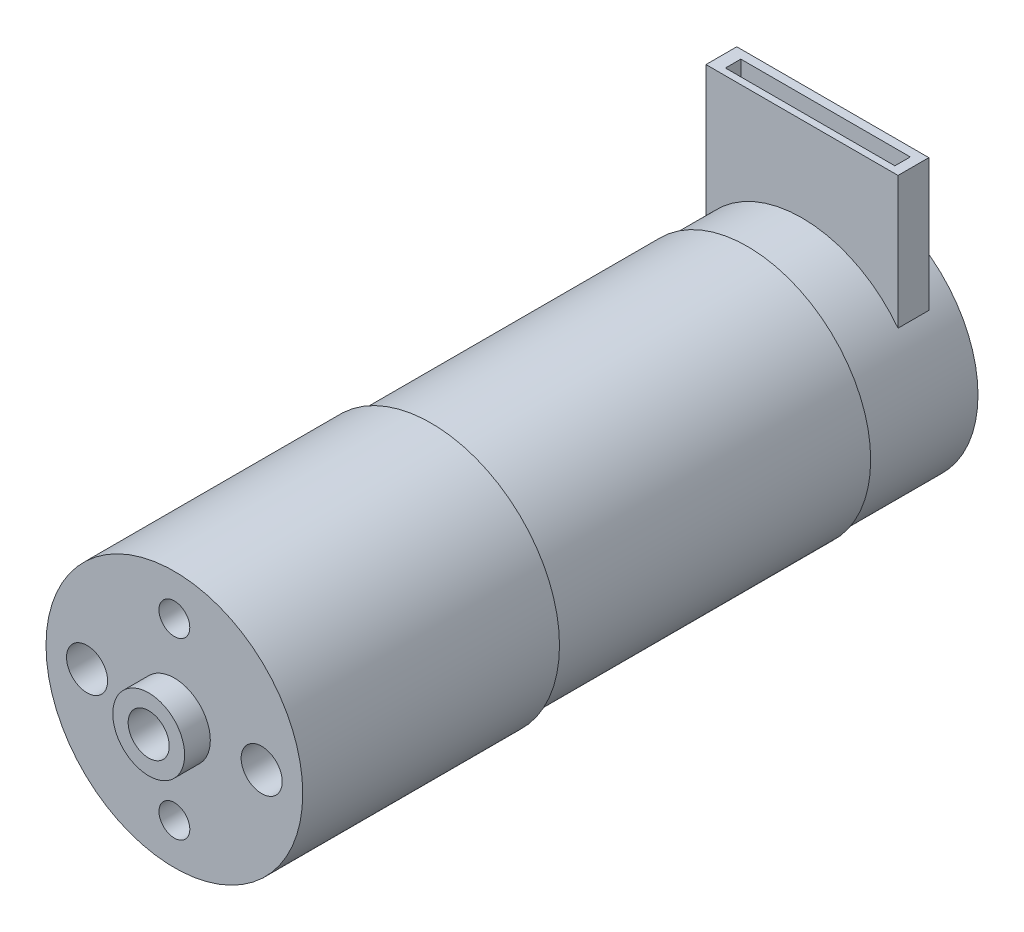
SolidWorks part; units mm, degrees
material "1060 Alloy"
ref_plane "Front Plane" through (0, 0, 0) normal (0, 0, 1) x (1, 0, 0)
ref_plane "Top Plane" through (0, 0, 0) normal (0, 1, 0) x (1, 0, 0)
ref_plane "Right Plane" through (0, 0, 0) normal (1, 0, 0) x (0, 0, -1)
sketch "Sketch1" plane through (0, 0, 0) normal (0, 0, 1) x (1, 0, 0)
  circle A0 centre (0, 0) radius 12
  dimension "D1" = 24
extrude "Boss-Extrude1" add sketch "Sketch1" along normal blind 30.8
sketch "Sketch2" plane through (0, 0, 30.8) normal (0, 0, 1) x (1, 0, 0)
  circle A0 centre (0, 0) radius 12.5
  dimension "D1" = 25
extrude "Boss-Extrude2" add sketch "Sketch2" along normal blind 25
sketch "Sketch3" plane through (0, 0, 55.8) normal (0, 0, 1) x (1, 0, 0)
  circle A0 centre (0, 0) radius 3.5
  dimension "D1" = 7
extrude "Boss-Extrude3" add sketch "Sketch3" along normal blind 2.5
sketch "Sketch4" plane through (0, 0, 58.3) normal (0, 0, 1) x (1, 0, 0)
  circle A0 centre (0, 0) radius 2
  dimension "D1" = 4
sketch "Sketch6" plane through (0, 0, 0) normal (0, 0, -1) x (-1, 0, 0)
  circle A0 centre (0, 0) radius 11.75
  dimension "D1" = 23.5
extrude "Boss-Extrude5" add sketch "Sketch6" along normal blind 10.7
sketch "Sketch7" plane through (0, 0, 0) normal (0, 1, 0) x (1, 0, 0)
  line L1 (9.3497, 8.3124) -> (-9.3497, 8.3124)
  line L2 (9.3497, 8.3124) -> (9.3497, 5.3124)
  line L3 (9.3497, 5.3124) -> (-9.3497, 5.3124)
  line L4 (-9.3497, 8.3124) -> (-9.3497, 5.3124)
  line L5 (9.3497, 8.3124) -> (-9.3497, 5.3124) construction
  line L6 (9.3497, 5.3124) -> (-9.3497, 8.3124) construction
  point P0 (0, 6.8124)
  dimension "D1" = 18.6994
  dimension "D2" = 3
extrude "Boss-Extrude6" add sketch "Sketch7" along normal blind 20
sketch "Sketch10" plane through (0, 20, 0) normal (0, 1, 0) x (1, 0, 0)
  line L1 (8.3873, 7.4684) -> (-8.1127, 7.4684)
  line L2 (8.3873, 7.4684) -> (8.3873, 5.9684)
  line L3 (8.3873, 5.9684) -> (-8.1127, 5.9684)
  line L4 (-8.1127, 7.4684) -> (-8.1127, 5.9684)
  line L5 (8.3873, 7.4684) -> (-8.1127, 5.9684) construction
  line L6 (8.3873, 5.9684) -> (-8.1127, 7.4684) construction
  point P0 (0.1373, 6.7184)
  dimension "D1" = 16.5
  dimension "D2" = 1.5
extrude "Cut-Extrude4" cut sketch "Sketch10" against normal blind 10
extrude "Cut-Extrude7" cut sketch "Sketch4" against normal blind 10
sketch "Sketch11" plane through (0, 0, 55.8) normal (0, 0, 1) x (1, 0, 0)
  line L0 (0, 0) -> (8.5, 0) construction
  line L1 (0, 0) -> (0, 8.5) construction
  circle A0 centre (0, 8.5) radius 1.5
  circle A1 centre (8.5, 0) radius 2
  circle A2 centre (-8.5, 0) radius 2
  circle A3 centre (0, -8.5) radius 1.5
  dimension "D3" = 3
  dimension "D4" = 4
  dimension "D1" = 8.5
  dimension "D2" = 8.5
extrude "Cut-Extrude8" cut sketch "Sketch11" against normal blind 10
